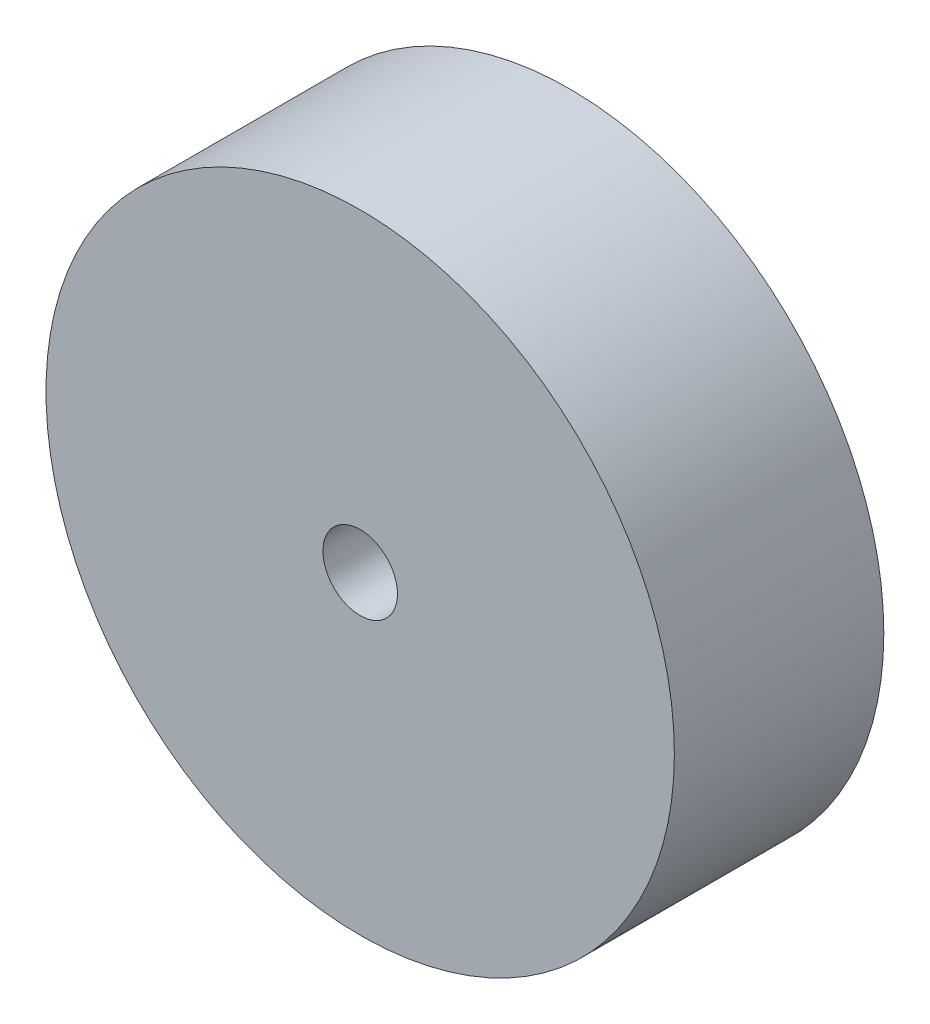
SolidWorks part; units mm, degrees
material "Brass"
ref_plane "Front Plane" through (0, 0, 0) normal (0, 0, 1) x (1, 0, 0)
ref_plane "Top Plane" through (0, 0, 0) normal (0, 1, 0) x (1, 0, 0)
ref_plane "Right Plane" through (0, 0, 0) normal (1, 0, 0) x (0, 0, -1)
sketch "Sketch1" plane through (0, 0, 0) normal (0, 0, 1) x (1, 0, 0)
  circle A0 centre (0, 0) radius 9.525
  dimension "D1" = 19.05
extrude "Boss-Extrude1" add sketch "Sketch1" along normal blind 6.35
hole_wizard "#4-40 Tapped Hole1" positions "Sketch2" profile "Sketch3" tap size "#4-40" standard "ANSI Inch" end condition through all
sketch "Sketch2" plane through (0, 0, 6.35) normal (0, 0, 1) x (1, 0, 0)
  point P0 (0, 0)
sketch "Sketch3" plane through (0, 0, 6.35) normal (1, 0, 0) x (0, -1, 0)
  line L0 (0, 0) -> (0, 6.35)
  line L1 (0, 6.35) -> (1.1303, 6.35)
  line L2 (1.1303, 6.35) -> (1.1303, 0)
  line L5 (1.1303, 0) -> (0, 0)
  line L11 (0, -6.35) -> (0, 107.95) construction
  dimension "Thru Tap Drill Dia." = 2.2606
  dimension "Thru Tap Drill Depth" = 6.35
cosmetic thread "Hole Thread1" parameters "D2"=2.8448
